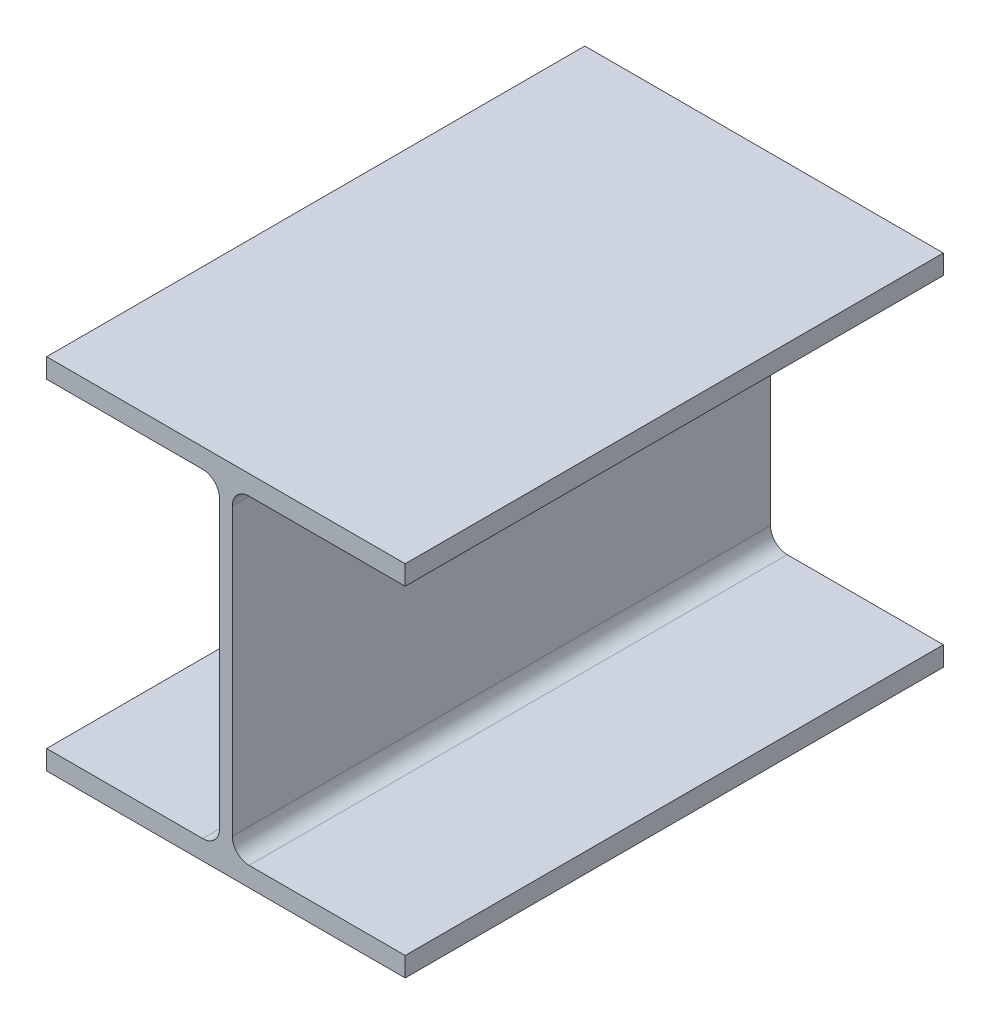
SolidWorks part; units mm, degrees
material "ASTM A36 Steel"
ref_plane "Front Plane" through (0, 0, 0) normal (0, 0, 1) x (1, 0, 0)
ref_plane "Top Plane" through (0, 0, 0) normal (0, 1, 0) x (1, 0, 0)
ref_plane "Right Plane" through (0, 0, 0) normal (1, 0, 0) x (0, 0, -1)
sketch "Sketch2" plane through (0, 0, 0) normal (0, 0, 1) x (1, 0, 0)
  line L0 (0, 0) -> (0, 145.1473) construction
  line L1 (0, 0) -> (205.4033, 0) construction
  line L2 (-3.6195, 90.551) -> (-3.6195, -90.551)
  line L3 (-101.5365, 101.6) -> (101.5365, 101.6)
  line L4 (-101.5365, 101.6) -> (-101.5365, 90.551)
  line L5 (-101.5365, 90.551) -> (-3.6195, 90.551)
  line L6 (101.5365, 101.6) -> (101.5365, 90.551)
  line L7 (-101.5365, -90.551) -> (-3.6195, -90.551)
  line L8 (-101.5365, -90.551) -> (-101.5365, -101.6)
  line L9 (-101.5365, -101.6) -> (101.5365, -101.6)
  line L10 (101.5365, -90.551) -> (101.5365, -101.6)
  line L11 (3.6195, 90.551) -> (3.6195, -90.551)
  line L12 (3.6195, -90.551) -> (101.5365, -90.551)
  line L13 (3.6195, 90.551) -> (101.5365, 90.551)
  dimension "D1" = 203.073
  dimension "D2" = 11.049
  dimension "D3" = 203.2
  dimension "D4" = 7.239
extrude "Boss-Extrude1" add sketch "Sketch2" along normal mid plane 304.8 contours L7 L2 L5 L4 L3 L6 L13 L11 L12 L10 L9 L8
fillet "Fillet1" radius 9.525
